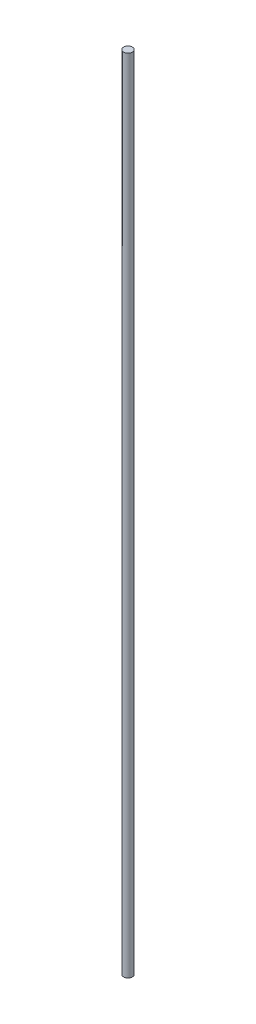
SolidWorks part; units mm, degrees
ref_plane "Front Plane" through (0, 0, 0) normal (0, 0, 1) x (1, 0, 0)
ref_plane "Top Plane" through (0, 0, 0) normal (0, 1, 0) x (1, 0, 0)
ref_plane "Right Plane" through (0, 0, 0) normal (1, 0, 0) x (0, 0, -1)
sketch "Sketch1" plane through (0, 0, 0) normal (0, 1, 0) x (1, 0, 0)
  circle A0 centre (0, 0) radius 0.95
extrude "Boss-Extrude1" add sketch "Sketch1" along normal blind 173
